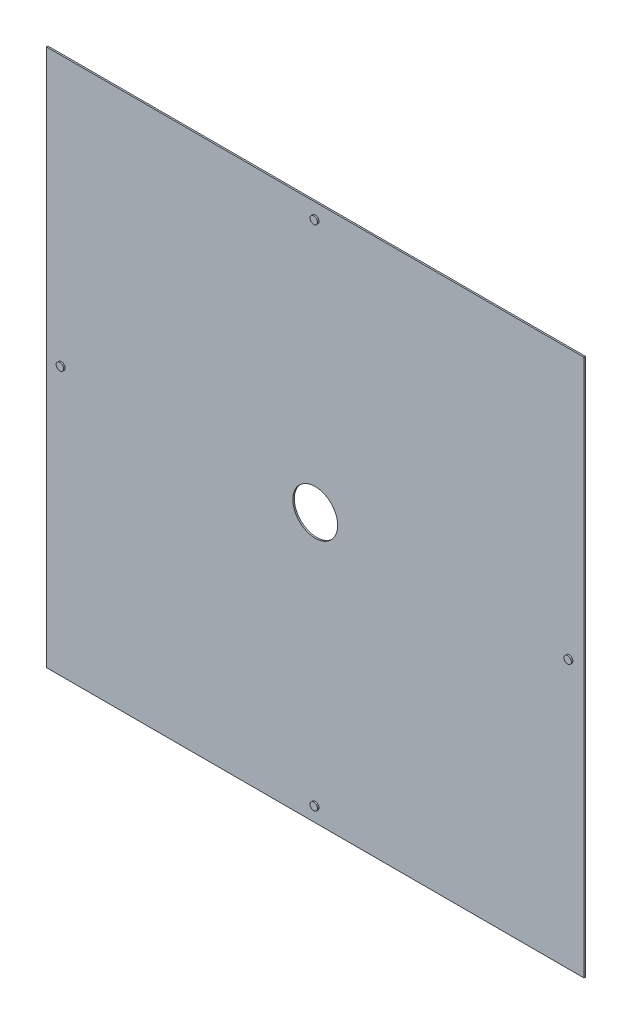
SolidWorks part; units mm, degrees
ref_plane "Front" through (0, 0, 0) normal (0, 0, 1) x (1, 0, 0)
ref_plane "Top" through (0, 0, 0) normal (0, 1, 0) x (1, 0, 0)
ref_plane "Right" through (0, 0, 0) normal (1, 0, 0) x (0, 0, -1)
sketch "Sketch2" plane through (0, 0, 0) normal (0, 0, 1) x (1, 0, 0)
  line L1 (-360, 360) -> (360, 360)
  line L2 (-360, 360) -> (-360, -360)
  line L3 (-360, -360) -> (360, -360)
  line L4 (360, 360) -> (360, -360)
  line L5 (-360, 360) -> (360, -360) construction
  line L6 (-360, -360) -> (360, 360) construction
  circle A0 centre (0, 0) radius 30
  point P0 (0, 0)
  dimension "D3" = 60
  dimension "D1" = 720
  dimension "D2" = 720
extrude "Boss-Extrude1" add sketch "Sketch2" along normal blind 2
sketch "Sketch3" plane through (0, 0, 2) normal (0, 0, 1) x (1, 0, 0)
  line L0 (-64.0866, 0) -> (74.0741, 0) construction
  line L1 (0, 80.7324) -> (0, -70.7449) construction
  line L2 (360, 360) -> (-360, 360) construction
  line L4 (-360, 360) -> (-360, -360) construction
  circle A0 centre (0, 340) radius 5
  circle A1 centre (-340, 0) radius 5
  circle A2 centre (0, -340) radius 5
  circle A3 centre (340, 0) radius 5
  dimension "D1" = 10
  dimension "D4" = 10
  dimension "D2" = 20
  dimension "D3" = 0
  dimension "D5" = 20
  dimension "D6" = 0
extrude "Boss-Extrude2" add sketch "Sketch3" along normal blind 2
